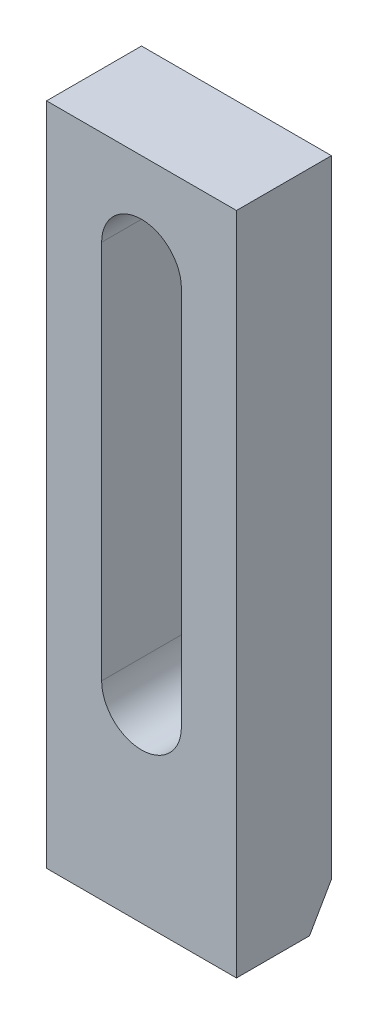
SolidWorks part; units mm, degrees
material "Простая углеродистая сталь"
ref_plane "Спереди" through (0, 0, 0) normal (0, 0, 1) x (1, 0, 0)
ref_plane "Сверху" through (0, 0, 0) normal (0, 1, 0) x (1, 0, 0)
ref_plane "Справа" through (0, 0, 0) normal (1, 0, 0) x (0, 0, -1)
sketch "Эскиз1" plane through (0, 0, 0) normal (0, 0, 1) x (1, 0, 0)
  line L1 (0, 0) -> (50, 0)
  line L2 (0, 0) -> (0, 175)
  line L3 (0, 175) -> (50, 175)
  line L4 (50, 0) -> (50, 175)
  dimension "D1" = 50
  dimension "D2" = 175
extrude "Бобышка-Вытянуть1" add sketch "Эскиз1" along normal blind 25
sketch "Эскиз2" plane through (0, 0, 25) normal (0, 0, 1) x (1, 0, 0)
  line L1 (14.5, 50) -> (14.5, 150)
  line L2 (35.5, 50) -> (35.5, 150)
  line L3 (0, 175) -> (0, 0) construction
  line L4 (0, 0) -> (50, 0) construction
  arc A0 (14.5, 50) -> (35.5, 50) centre (25, 50) ccw
  arc A1 (14.5, 150) -> (35.5, 150) centre (25, 150) cw
  point P7 (14.5, 100)
  point P10 (35.5, 100)
  dimension "D1" = 25
  dimension "D2" = 50
extrude "Вырез-Вытянуть1" cut sketch "Эскиз2" against normal through all
chamfer "Фаска1" distance 10 angle 30 1 edges at (25, 0, 0)
